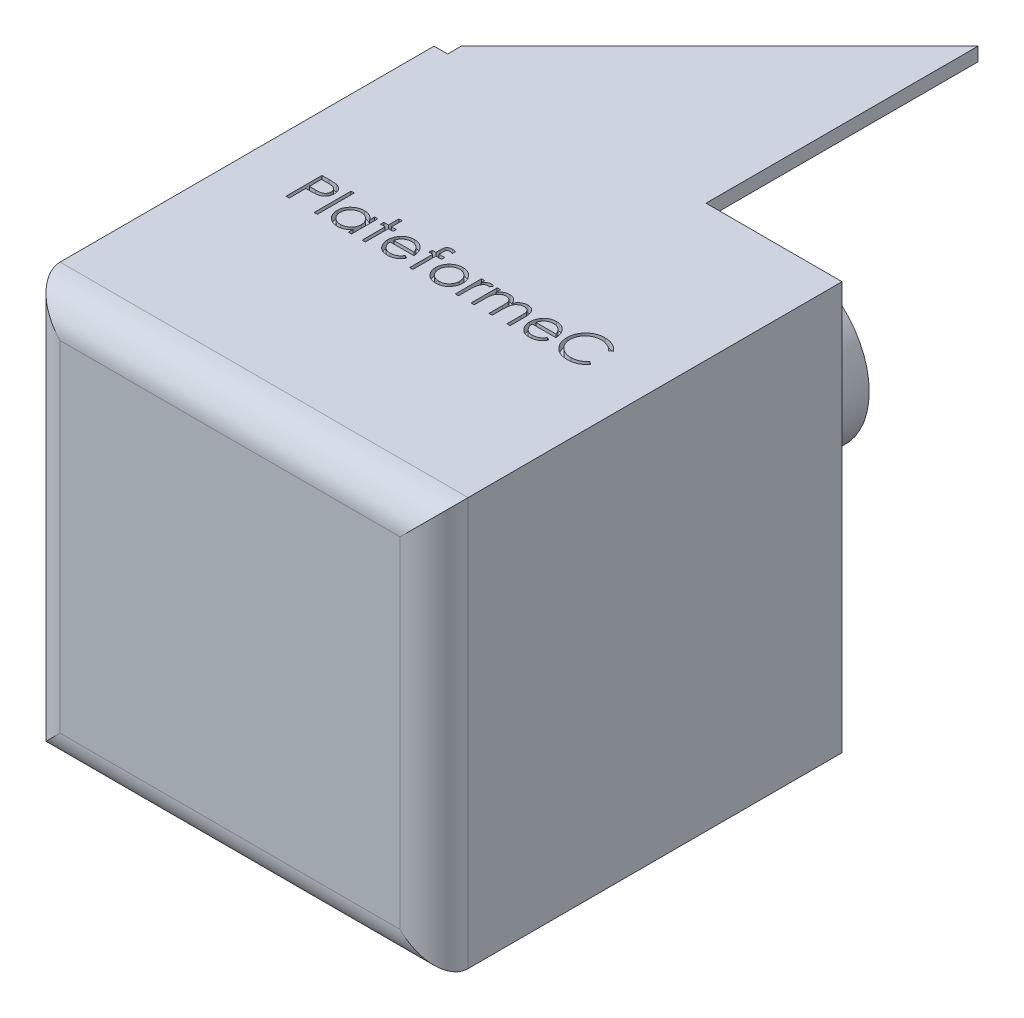
SolidWorks part; units mm, degrees
ref_plane "Plan de face" through (0, 0, 0) normal (0, 0, 1) x (1, 0, 0)
ref_plane "Plan de dessus" through (0, 0, 0) normal (0, 1, 0) x (1, 0, 0)
ref_plane "Plan de droite" through (0, 0, 0) normal (1, 0, 0) x (0, 0, -1)
sketch "Esquisse1" plane through (0, 0, 0) normal (0, 0, 1) x (1, 0, 0)
  line L1 (0, 0) -> (-60, 0)
  line L2 (0, 0) -> (0, 60)
  line L3 (0, 60) -> (-60, 60)
  line L4 (-60, 0) -> (-60, 60)
  dimension "D1" = 60
  dimension "D2" = 60
extrude "Boss.-Extru.1" add sketch "Esquisse1" along normal blind 60
sketch "Esquisse2" plane through (0, 0, 0) normal (0, 0, -1) x (-1, 0, 0)
  line L0 (60, 60) -> (60, 0) construction
  line L1 (0, 60) -> (60, 60) construction
  circle A0 centre (28, 28) radius 12
  dimension "D1" = 24
  dimension "D2" = 32
  dimension "D3" = 32
sketch "Esquisse3" plane through (0, 0, 0) normal (0, 0, -1) x (-1, 0, 0)
  line L0 (60, 60) -> (60, 20)
  line L1 (60, 60) -> (60, 0) construction
  line L2 (60, 20) -> (58, 20)
  line L3 (58, 20) -> (58, 58)
  line L4 (58, 58) -> (20, 58)
  line L5 (20, 58) -> (20, 60)
  line L6 (0, 60) -> (60, 60) construction
  line L7 (20, 60) -> (60, 60)
  dimension "D1" = 40
  dimension "D2" = 40
  dimension "D3" = 2
  dimension "D4" = 2
extrude "Boss.-Extru.3" add sketch "Esquisse3" along normal blind 40
extrude "Boss.-Extru.4" add sketch "Esquisse2" along normal blind 20
sketch "Esquisse6" plane through (-60, 0, 0) normal (-1, 0, 0) x (0, 0, 1)
  line L0 (30, 0) -> (30, 60) construction
  line L1 (60, 0) -> (0, 0) construction
  line L2 (60, 60) -> (-40, 60) construction
  text T0 "PING" font "Century Gothic" height in points 48
extrude "Enlèv. mat.-Extru.3" cut sketch "Esquisse6" against normal blind 1
sketch "Esquisse7" plane through (0, 60, 0) normal (0, 1, 0) x (1, 0, 0)
  line L0 (0, -30) -> (-60, -30) construction
  line L1 (0, -60) -> (0, 0) construction
  line L2 (-60, -60) -> (-60, 40) construction
  text T0 "PlateformeC" font "Century Gothic" height in points 20
extrude "Enlèv. mat.-Extru.4" cut sketch "Esquisse7" against normal blind 1
sketch "Esquisse8" plane through (-60, 0, 0) normal (-1, 0, 0) x (0, 0, 1)
  line L0 (-40, 20) -> (0, 60)
  line L1 (60, 60) -> (-40, 60) construction
  line L2 (0, 60) -> (-40, 60)
  line L3 (-40, 60) -> (-40, 20)
  dimension "D1" = 45
extrude "Enlèv. mat.-Extru.5" cut sketch "Esquisse8" against normal blind 2
sketch "Esquisse11" plane through (0, 60, 0) normal (0, 1, 0) x (1, 0, 0)
  line L0 (-20, 40) -> (-60, 0)
  line L1 (-60, 0) -> (-61.461, 41.461)
  line L2 (-61.461, 41.461) -> (-20, 40)
extrude "Enlèv. mat.-Extru.6" cut sketch "Esquisse11" against normal blind 2
fillet "Congé1" radius 5 4 edges at (-60, 30, 60) (-30, 0, 60) (0, 30, 60) (-30, 60, 60)
